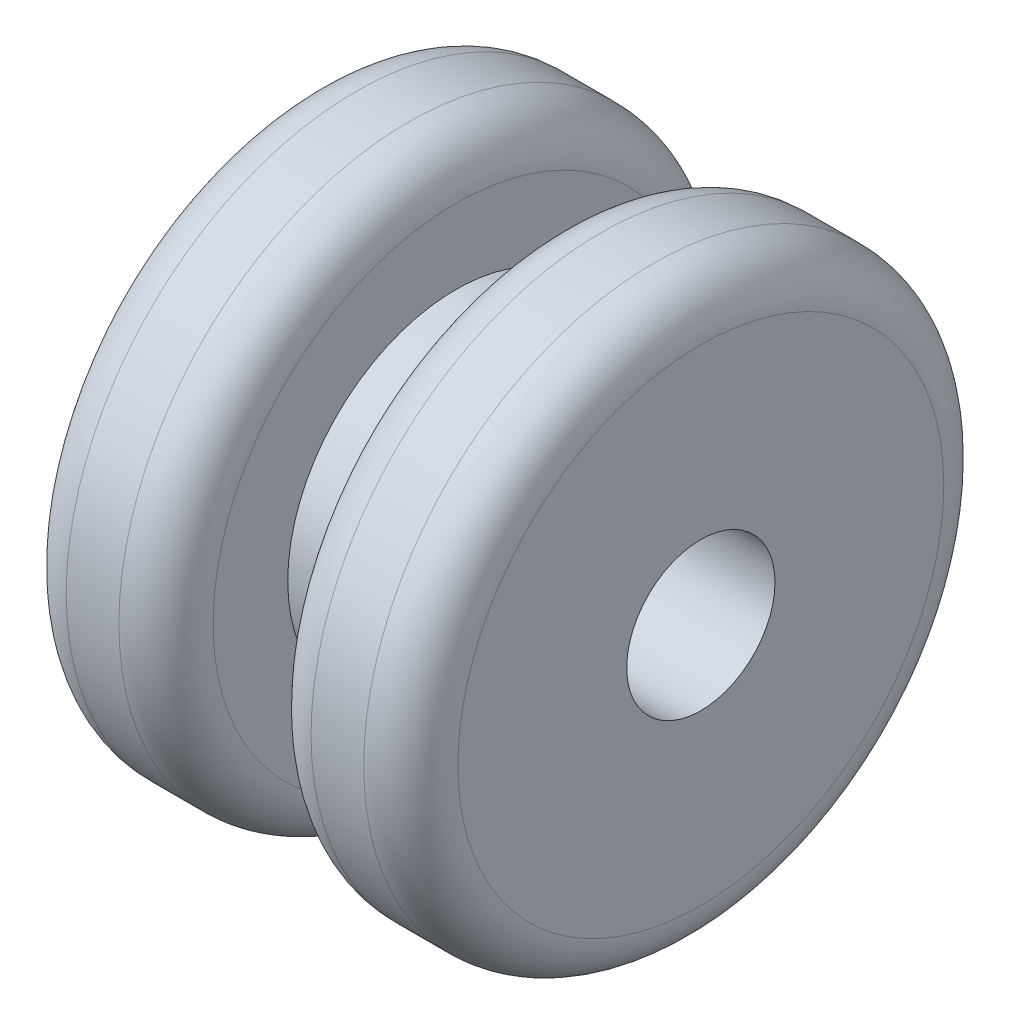
SolidWorks part; units mm, degrees
ref_plane "Front Plane" through (0, 0, 0) normal (0, 0, 1) x (1, 0, 0)
ref_plane "Top Plane" through (0, 0, 0) normal (0, 1, 0) x (1, 0, 0)
ref_plane "Right Plane" through (0, 0, 0) normal (1, 0, 0) x (0, 0, -1)
sketch "Sketch1" plane through (0, 0, 0) normal (1, 0, 0) x (0, 0, -1)
  circle A0 centre (0, 0) radius 9.779
  circle A1 centre (0, 0) radius 2.5
  dimension "D1" = 5
  dimension "D2" = 19.558
extrude "Boss-Extrude1" add sketch "Sketch1" along normal mid plane 13.208
sketch "Sketch2" plane through (0, 0, 0) normal (1, 0, 0) x (0, 0, -1)
  circle A0 centre (0, 0) radius 5.675
  circle A1 centre (0, 0) radius 11.049
  circle A2 centre (0, 0) radius 9.779 construction
  circle A3 centre (0, 0) radius 2.5 construction
  dimension "D1" = 1.27
  dimension "D2" = 3.175
extrude "Cut-Extrude1" cut sketch "Sketch2" against normal mid plane 3.302
fillet "Fillet1" radius 1.5875 4 edges at (6.604, 0, -9.779) (1.651, 0, -9.779) (-1.651, 0, -9.779) (-6.604, 0, -9.779)
